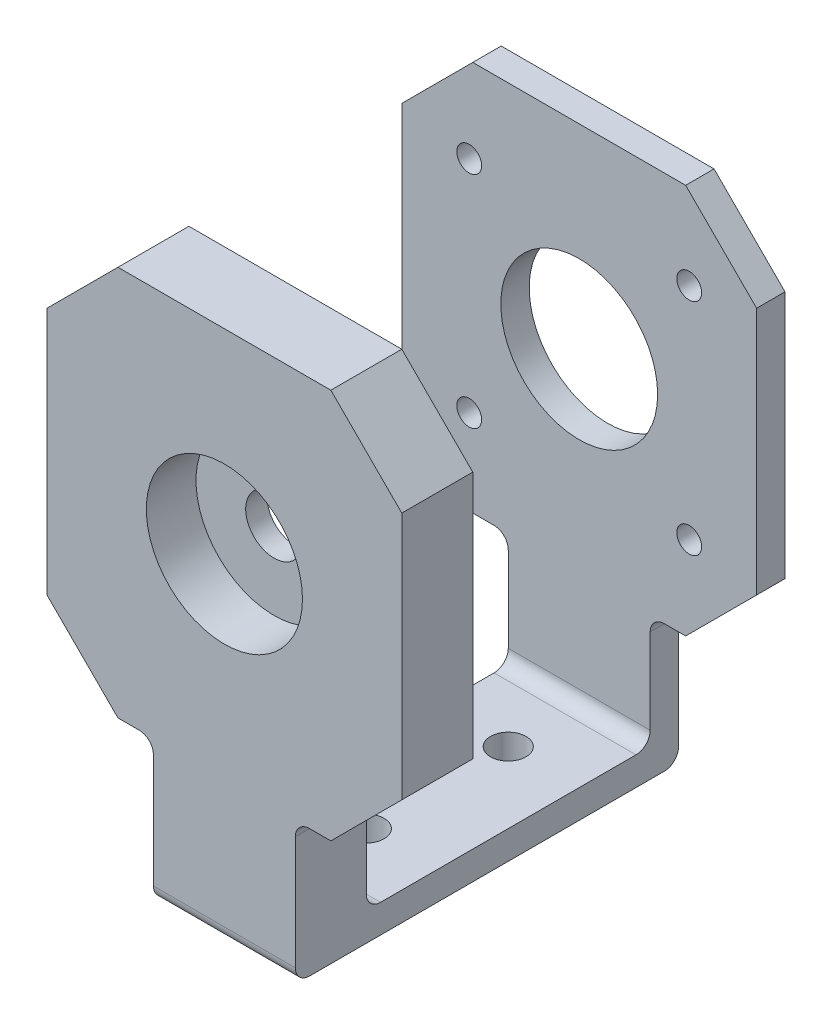
SolidWorks part; units mm, degrees
material "PLA"
ref_plane "Piano frontale" through (0, 0, 0) normal (0, 0, 1) x (1, 0, 0)
ref_plane "Piano superiore" through (0, 0, 0) normal (0, 1, 0) x (1, 0, 0)
ref_plane "Piano destro" through (0, 0, 0) normal (1, 0, 0) x (0, 0, -1)
sketch "Schizzo1" plane through (0, 0, 0) normal (0, 0, 1) x (1, 0, 0)
  line L5 (0, 0) -> (0, -67.5867) construction
  line L6 (-25, -27.5) -> (-10, -27.5)
  line L10 (-25, -27.5) -> (-25, 27.5)
  line L11 (-15.5, 15.5) -> (15.5, 15.5) construction
  line L12 (-15.5, 15.5) -> (-15.5, -15.5) construction
  line L13 (-15.5, -15.5) -> (15.5, -15.5) construction
  line L14 (15.5, 15.5) -> (15.5, -15.5) construction
  line L15 (-15.5, 15.5) -> (15.5, -15.5) construction
  line L16 (-15.5, -15.5) -> (15.5, 15.5) construction
  line L17 (-25, 27.5) -> (25, 27.5)
  line L18 (25, -27.5) -> (25, 27.5)
  line L22 (-25, -27.5) -> (25, 27.5) construction
  line L27 (-25, 27.5) -> (25, -27.5) construction
  line L29 (-10, -47.5) -> (10, -47.5)
  line L31 (-10, -47.5) -> (-10, -27.5)
  line L33 (10, -47.5) -> (10, -27.5)
  line L34 (-10, -47.5) -> (10, -27.5) construction
  line L35 (-10, -27.5) -> (10, -47.5) construction
  line L36 (10, -27.5) -> (25, -27.5)
  circle A0 centre (-15.5, 15.5) radius 1.75
  circle A1 centre (15.5, 15.5) radius 1.75
  circle A2 centre (15.5, -15.5) radius 1.75
  circle A3 centre (-15.5, -15.5) radius 1.75
  circle A4 centre (0, 0) radius 11.05
  point P4 (0, -37.5)
  point P14 (0, 0)
  dimension "D10" = 3.5
  dimension "D11" = 22.1
  dimension "D2" = 50
  dimension "D4" = 20
  dimension "D3" = 55
  dimension "D8" = 31
  dimension "D5" = 20
extrude "Estrusione-Estrusione1" add sketch "Schizzo1" along normal blind 4
sketch "Schizzo14" plane through (0, 0, 4) normal (0, 0, 1) x (1, 0, 0)
  line L0 (10, -47.5) -> (10, -27.5) construction
  line L1 (-10, -47.5) -> (10, -47.5)
  line L2 (-10, -47.5) -> (-10, -43.5)
  line L3 (-10, -43.5) -> (10, -43.5)
  line L4 (10, -47.5) -> (10, -43.5)
  dimension "D1" = 4
extrude "Estrusione-Estrusione2" add sketch "Schizzo14" along normal blind 40
sketch "Schizzo18" plane through (0, 0, 44) normal (0, 0, 1) x (1, 0, 0)
  line L0 (0, 0) -> (0, -60.5983) construction
  line L1 (-25, -27.5) -> (-10, -27.5)
  line L2 (-25, -27.5) -> (-25, 27.5)
  line L9 (-25, 27.5) -> (25, 27.5)
  line L10 (25, -27.5) -> (25, 27.5)
  line L11 (-25, -27.5) -> (25, 27.5) construction
  line L12 (-25, 27.5) -> (25, -27.5) construction
  line L13 (-10, -47.5) -> (10, -47.5)
  line L14 (-10, -47.5) -> (-10, -27.5)
  line L15 (10, -47.5) -> (10, -27.5)
  line L16 (-10, -47.5) -> (10, -27.5) construction
  line L17 (-10, -27.5) -> (10, -47.5) construction
  line L18 (10, -27.5) -> (25, -27.5)
  point P4 (0, -37.5)
  dimension "D4" = 50
  dimension "D5" = 55
  dimension "D6" = 20
  dimension "D7" = 20
extrude "Estrusione-Estrusione3" add sketch "Schizzo18" along normal blind 10
sketch "Schizzo19" plane through (0, 0, 54) normal (0, 0, 1) x (1, 0, 0)
  circle A0 centre (0, 0) radius 11
  dimension "D1" = 22
extrude "Taglio-Estrusione1" cut sketch "Schizzo19" against normal blind 7
sketch "Schizzo20" plane through (0, 0, 47) normal (0, 0, 1) x (1, 0, 0)
  circle A0 centre (0, 0) radius 4
  dimension "D1" = 8
extrude "Taglio-Estrusione2" cut sketch "Schizzo20" against normal blind 7
chamfer "Smusso1" distance 10 angle 45 8 edges at (25, 27.5, 2) (25, -27.5, 2) (-25, -27.5, 2) (-25, 27.5, 2) (25, -27.5, 49) (-25, -27.5, 49) (-25, 27.5, 49) (25, 27.5, 49)
fillet "Raccordo1" radius 2 8 edges at (0, -47.5, 0) (-10, -27.5, 2) (10, -27.5, 2) (0, -43.5, 4) (0, -43.5, 44) (0, -47.5, 54) (-10, -27.5, 49) (10, -27.5, 49)
sketch "Schizzo21" plane through (0, -43.5, 0) normal (0, 1, 0) x (1, 0, 0)
  line L0 (0, 0) -> (0, -54) construction
  line L1 (15, -54) -> (-15, -54) construction
  line L2 (-10, -24) -> (10, -24) construction
  line L3 (-10, -42) -> (-10, -6) construction
  line L4 (10, -42) -> (10, -6) construction
  line L5 (-10, -4) -> (10, -4) construction
  circle A0 centre (0, -14) radius 2.5
  circle A1 centre (0, -34) radius 2.5
  dimension "D1" = 10
  dimension "D2" = 5
extrude "Taglio-Estrusione3" cut sketch "Schizzo21" against normal blind 10
